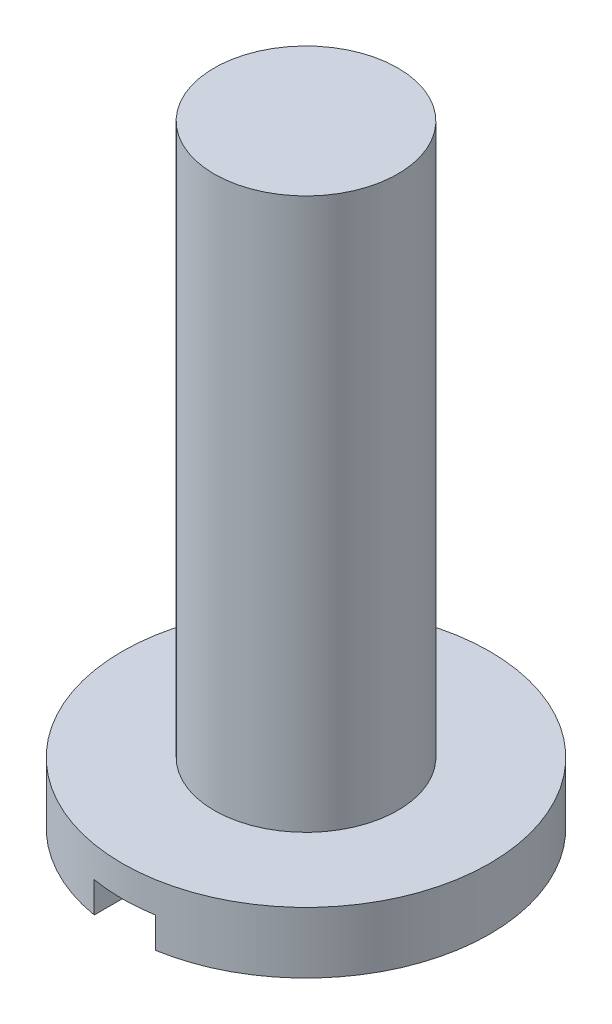
SolidWorks part; units mm, degrees
ref_plane "Plan de face" through (0, 0, 0) normal (0, 0, 1) x (1, 0, 0)
ref_plane "Plan de dessus" through (0, 0, 0) normal (0, 1, 0) x (1, 0, 0)
ref_plane "Plan de droite" through (0, 0, 0) normal (1, 0, 0) x (0, 0, -1)
sketch "Esquisse1" plane through (0, 0, 0) normal (0, 0, 1) x (1, 0, 0)
  line L0 (0, 0) -> (0, 55.7854) construction
  line L1 (0, 0) -> (3, 0)
  line L2 (3, 0) -> (3, 1)
  line L3 (3, 1) -> (1.5, 1)
  line L4 (1.5, 1) -> (1.5, 10)
  line L5 (1.5, 10) -> (0, 10)
  line L6 (0, 10) -> (0, 0)
  dimension "D1" = 3
  dimension "D2" = 1.5
  dimension "D3" = 1
  dimension "D4" = 10
revolve "Révolution1" add sketch "Esquisse1" angle 360 about L0
sketch "Esquisse2" plane through (0, 0, 0) normal (0, -1, 0) x (1, 0, 0)
  line L1 (-0.5, 3) -> (0.5, 3)
  line L2 (-0.5, 3) -> (-0.5, -3)
  line L3 (-0.5, -3) -> (0.5, -3)
  line L4 (0.5, 3) -> (0.5, -3)
  circle A0 centre (0, 0) radius 3 construction
  dimension "D1" = 1
  dimension "D2" = 0.5
extrude "Enlèv. mat.-Extru.1" cut sketch "Esquisse2" against normal blind 0.5
